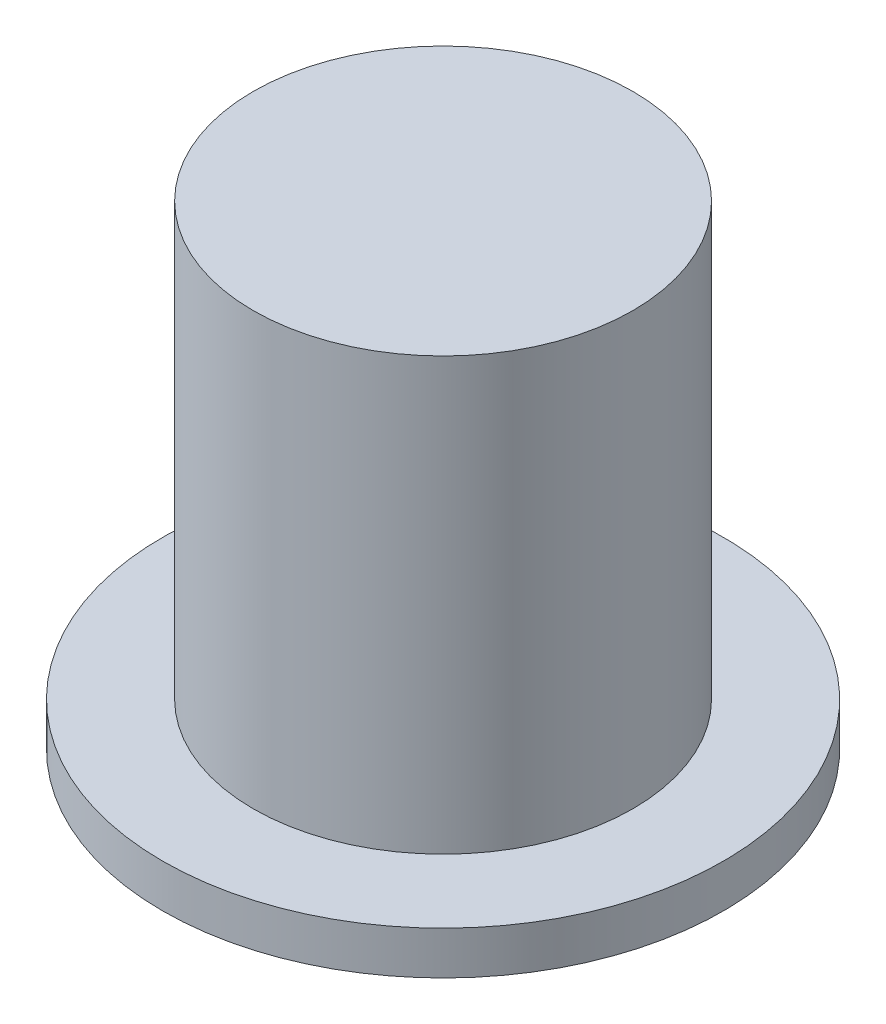
SolidWorks part; units mm, degrees
ref_plane "Front Plane" through (0, 0, 0) normal (0, 0, 1) x (1, 0, 0)
ref_plane "Top Plane" through (0, 0, 0) normal (0, 1, 0) x (1, 0, 0)
ref_plane "Right Plane" through (0, 0, 0) normal (1, 0, 0) x (0, 0, -1)
sketch "Sketch1" plane through (0, 0, 0) normal (0, 1, 0) x (1, 0, 0)
  circle A0 centre (0, 0) radius 3.25
  dimension "D1" = 6.5
extrude "Boss-Extrude1" add sketch "Sketch1" along normal blind 0.5
sketch "Sketch2" plane through (0, 0.5, 0) normal (0, 1, 0) x (1, 0, 0)
  circle A0 centre (0, 0) radius 2.2
  dimension "D1" = 4.4
extrude "Boss-Extrude2" add sketch "Sketch2" along normal blind 5
